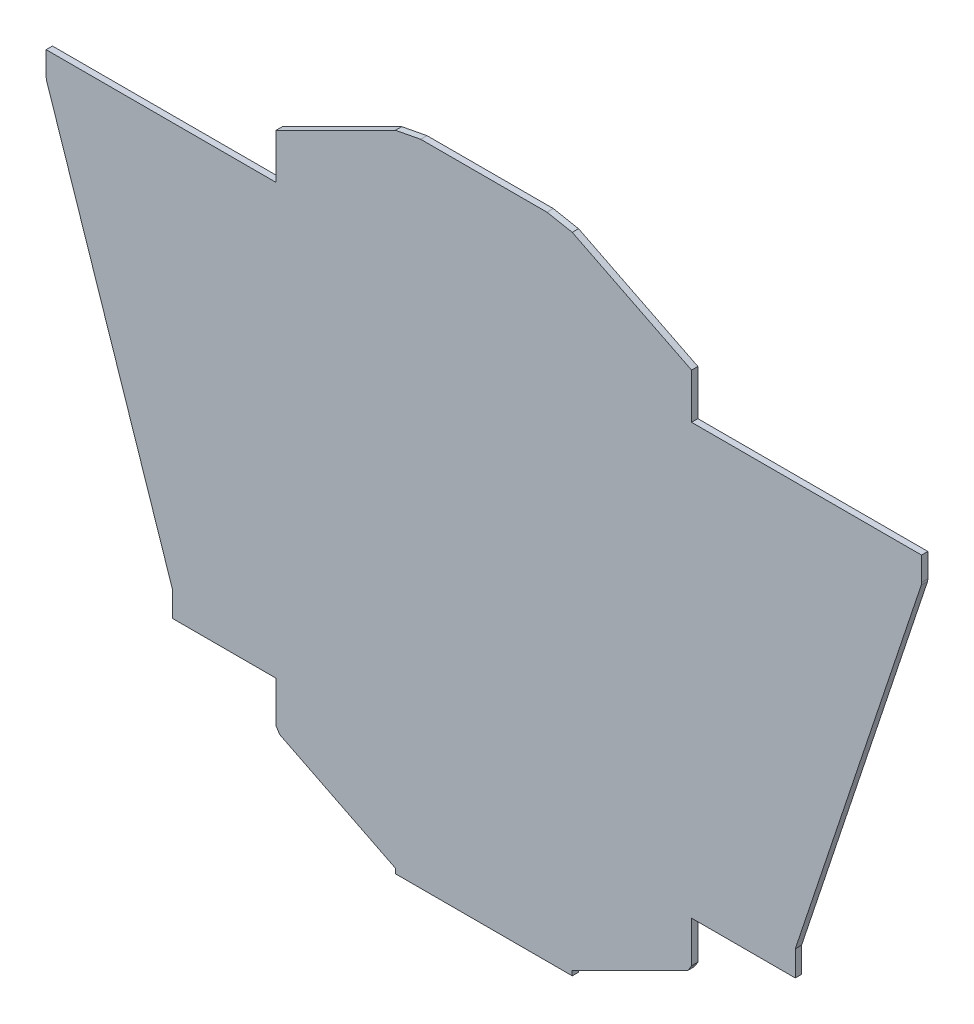
SolidWorks part; units mm, degrees
ref_plane "Front Plane" through (0, 0, 0) normal (0, 0, 1) x (1, 0, 0)
ref_plane "Top Plane" through (0, 0, 0) normal (0, 1, 0) x (1, 0, 0)
ref_plane "Right Plane" through (0, 0, 0) normal (1, 0, 0) x (0, 0, -1)
sketch "Sketch1" plane through (0, 0, 0) normal (0, 0, 1) x (1, 0, 0)
  line L0 (-207.5699, -422.4085) -> (-37.1068, -422.4085)
  line L1 (-207.5699, -422.4085) -> (-245.6699, -422.4085)
  line L2 (-245.6699, -422.4085) -> (-245.6699, -371.6085)
  line L3 (-245.6699, -371.6085) -> (-499.0181, 388.4363)
  line L4 (-499.0181, 388.4363) -> (-499.6699, 393.8659)
  line L5 (-499.6699, 393.8659) -> (-499.6699, 441.1915)
  line L6 (-461.5699, 441.1915) -> (-499.6699, 441.1915)
  line L7 (-461.5699, 441.1915) -> (-37.1068, 441.1915)
  line L8 (-37.1068, 441.1915) -> (-37.1068, 532.0653)
  line L9 (-37.1068, 532.0653) -> (202.8525, 652.0449)
  line L10 (202.8525, 652.0449) -> (253.6525, 661.7468)
  line L11 (253.6525, 661.7468) -> (380.6525, 661.7468)
  line L12 (380.6525, 661.7468) -> (380.6525, -642.9639)
  line L13 (380.6525, -642.9639) -> (202.8525, -642.9639)
  line L14 (202.8525, -642.9639) -> (202.8525, -633.2619)
  line L15 (202.8525, -633.2619) -> (-30.0864, -516.7925)
  line L16 (-30.0864, -516.7925) -> (-37.1068, -505.4333)
  line L17 (-37.1068, -505.4333) -> (-37.1068, -422.4085)
extrude "Boss-Extrude1" add sketch "Sketch1" along normal blind 12.7
mirror "Mirror1" about plane through (380.6525, 661.7468, 12.7) normal (-1, 0, 0) of bodies 101
